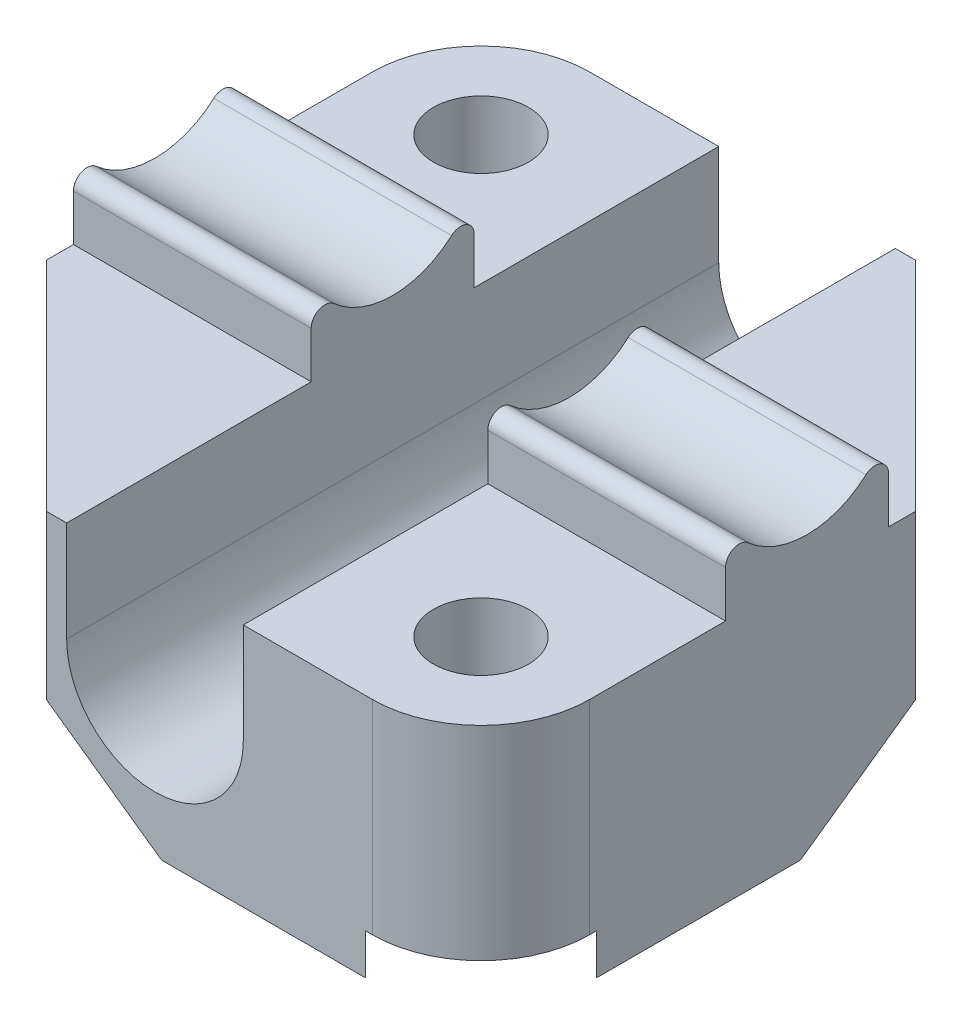
SolidWorks part; units mm, degrees
ref_plane "前视基准面" through (0, 0, 0) normal (0, 0, 1) x (1, 0, 0)
ref_plane "上视基准面" through (0, 0, 0) normal (0, 1, 0) x (1, 0, 0)
ref_plane "右视基准面" through (0, 0, 0) normal (1, 0, 0) x (0, 0, -1)
sketch "草图1" plane through (0, 0, 0) normal (0, 1, 0) x (1, 0, 0)
  line L1 (-12, -12) -> (12, -12)
  line L2 (-12, -12) -> (-12, 12)
  line L3 (-12, 12) -> (12, 12)
  line L4 (12, -12) -> (12, 12)
  line L5 (-12, -12) -> (12, 12) construction
  line L6 (-12, 12) -> (12, -12) construction
  point P0 (0, 0)
  dimension "D1" = 24
extrude "凸台-拉伸1" add sketch "草图1" along normal blind 10
sketch "草图2" plane through (0, 0, 12) normal (0, 0, 1) x (1, 0, 0)
  line L0 (0, 0) -> (0, 11.7448) construction
  line L2 (-12, 10) -> (12, 10) construction
  line L3 (-3.25, 6.3) -> (3.25, 6.3)
  line L4 (-3.25, 6.3) -> (-3.25, 10)
  line L5 (-3.25, 10) -> (3.25, 10)
  line L6 (3.25, 6.3) -> (3.25, 10)
  circle A0 centre (0, 6.3) radius 3.25
  line M5 (12, 10) -> (-12, 10)
  dimension "D1" = 6.5
  dimension "D2" = 3.7
extrude "切除-拉伸1" cut sketch "草图2" against normal through all and the other way through all contours A0 L0 L5 L4 | L0 A0 L6 M5 | L0 L3 A0 | L3 L0 A0 | A0 L0 L3 | L0 A0 L3
sketch "草图4" plane through (12, 0, 0) normal (1, 0, 0) x (0, 0, -1)
  line L0 (0, 0) -> (0, 12.1904) construction
  line L1 (-3, 13.25) -> (3, 13.25) construction
  line L2 (-12, 10) -> (12, 10) construction
  line L3 (-3, 10) -> (3, 10)
  line L4 (-3, 10) -> (-3, 13.25)
  line L6 (3, 10) -> (3, 13.25)
  arc A1 (-3, 13.25) -> (3, 13.25) centre (0, 14.5) ccw
  dimension "D2" = 6
  dimension "D1" = 3.25
  dimension "D3" = 4.5
extrude "凸台-拉伸2" add sketch "草图4" against normal blind 8.75 contours L6 A1 L4 L3
mirror "镜向2" about plane through (0, 0, 0) normal (1, 0, 0) of "凸台-拉伸2"
sketch "草图5" plane through (0, 10, 0) normal (0, 1, 0) x (1, 0, 0)
  line L0 (-12, 12) -> (12, -12) construction
  line L1 (-12, 12) -> (-12, 3) construction
  line L2 (0, 0) -> (12, 12) construction
  circle A0 centre (-8, 8) radius 1.75
  circle A1 centre (8, -8) radius 1.75
  dimension "D1" = 3.5
  dimension "D2" = 4
extrude "切除-拉伸3" cut sketch "草图5" against normal through all
chamfer "倒角1" distance 8 angle 45 2 edges at (12, 5, -12) (-12, 5, 12)
fillet "圆角1" radius 4 2 edges at (12, 5, 12) (-12, 5, -12)
fillet "圆角2" radius 0.5 4 edges at (7.625, 13.25, -3) (-7.625, 13.25, -3) (-7.625, 13.25, 3) (7.625, 13.25, 3)
chamfer "倒角2" distance 4 angle 45 2 edges at (8, 0, -8) (-8, 0, 8)
sketch "草图6" plane through (0, 0, 0) normal (0, -1, 0) x (1, 0, 0)
  line L0 (8, 8) -> (-8, -8) construction
  line L1 (-5.5505, -5.5505) -> (-8.8966, -4.6539)
  line L2 (-8.8966, -4.6539) -> (-11.3461, -7.1034)
  line L3 (-11.3461, -7.1034) -> (-10.4495, -10.4495)
  line L4 (-10.4495, -10.4495) -> (-7.1034, -11.3461)
  line L5 (-7.1034, -11.3461) -> (-4.6539, -8.8966)
  line L6 (-4.6539, -8.8966) -> (-5.5505, -5.5505)
  line L7 (0, 0) -> (5.1716, -5.1716) construction
  line L20 (-1.6569, -12) -> (12, 1.6569) construction
  line L21 (-11.3461, -7.1034) -> (-7.1034, -11.3461)
  line L22 (-11.3461, -7.1034) -> (-18.4171, -14.1745)
  line L23 (-7.1034, -11.3461) -> (-14.1745, -18.4171)
  line L24 (-18.4171, -14.1745) -> (-14.1745, -18.4171)
  line L25 (14.1745, 18.4171) -> (18.4171, 14.1745)
  line L26 (11.3461, 7.1034) -> (18.4171, 14.1745)
  line L27 (7.1034, 11.3461) -> (14.1745, 18.4171)
  line L28 (7.1034, 11.3461) -> (11.3461, 7.1034)
  line L29 (8.8966, 4.6539) -> (5.5505, 5.5505)
  line L30 (11.3461, 7.1034) -> (8.8966, 4.6539)
  line L31 (10.4495, 10.4495) -> (11.3461, 7.1034)
  line L32 (7.1034, 11.3461) -> (10.4495, 10.4495)
  line L33 (4.6539, 8.8966) -> (7.1034, 11.3461)
  line L34 (5.5505, 5.5505) -> (4.6539, 8.8966)
  circle A0 centre (-8, -8) radius 3 construction
  circle A1 centre (8, 8) radius 3 construction
  circle M23 centre (-8, -8) radius 1.75
  circle M24 centre (8, 8) radius 1.75
  line M25 (-8, -12) -> (-1.6569, -12)
  line M26 (12, 1.6569) -> (12, 8)
  arc M27 (12, 8) -> (8, 12) centre (8, 8) ccw
  line M28 (8, 12) -> (1.6569, 12)
  line M29 (-12, -1.6569) -> (-12, -8)
  arc M30 (-12, -8) -> (-8, -12) centre (-8, -8) ccw
  dimension "D1" = 10
  dimension "D2" = 6
extrude "切除-拉伸4" cut sketch "草图6" against normal blind 2.5 contours L2 L21 L5 L6 L1 M23 | L22 L24 L23 M25 M30 M29 | L21 L3 L4 M23 | L23 L4 L3 L22 M29 M30 M25 | L34 L29 L30 L28 L33 M24 | L32 L28 L31 M24 | L27 L32 L31 L26 M26 M27 M28 | L27 L26 L25 M28 M27 M26
chamfer "倒角3" distance 1 angle 45 4 edges at (12, 0, 4.7071) (4.7071, 0, 12) (-12, 0, -4.7071) (-4.7071, 0, -12)
